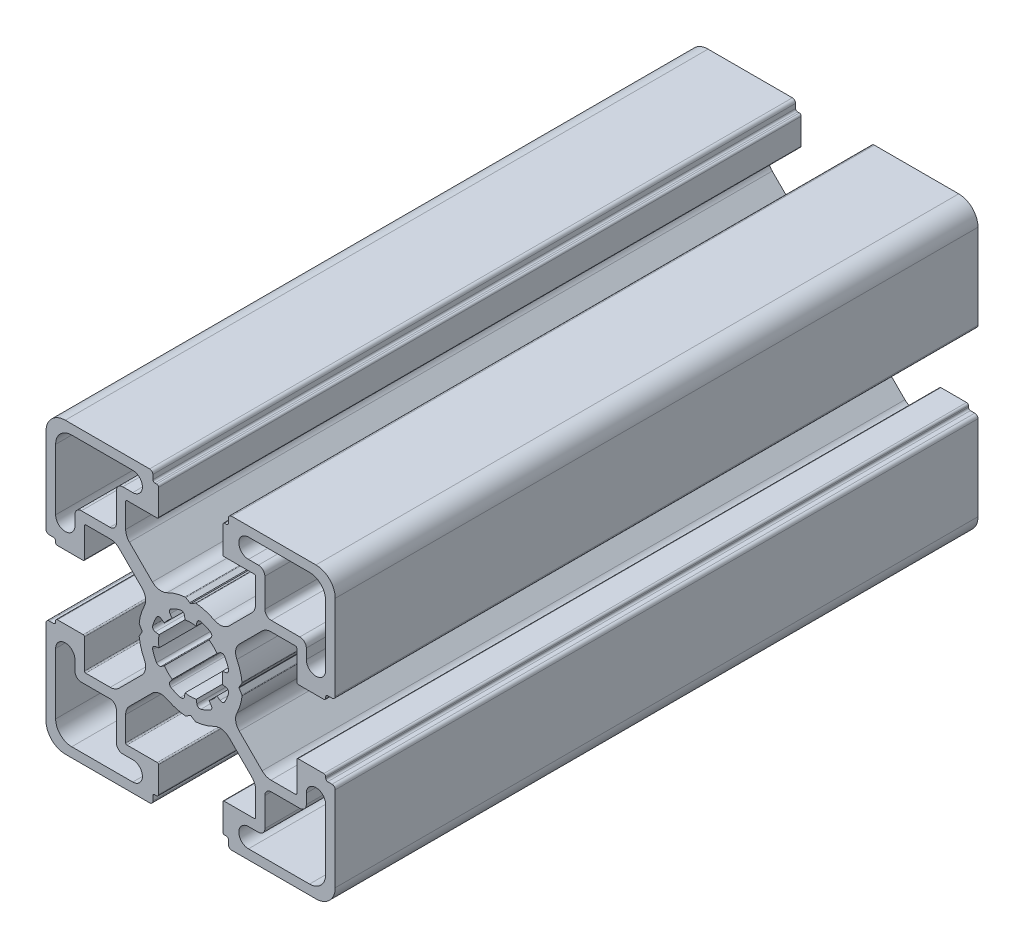
SolidWorks part; units mm, degrees
material "АД31 ГОСТ 4784-97"
ref_plane "Front Plane" through (0, 0, 0) normal (0, 0, 1) x (1, 0, 0)
ref_plane "Top Plane" through (0, 0, 0) normal (0, 1, 0) x (1, 0, 0)
ref_plane "Right Plane" through (0, 0, 0) normal (1, 0, 0) x (0, 0, -1)
sketch "Sketch1" plane through (0, 0, 0) normal (0, 0, 1) x (1, 0, 0)
  line L0 (10.55, 18) -> (9, 18)
  line L1 (18.5, 21) -> (9, 21)
  line L2 (21, 9.0002) -> (21, 18.5)
  line L3 (18, 9.0002) -> (18, 10.55)
  line L4 (17, 11.55) -> (12.55, 11.55)
  line L5 (11.55, 12.55) -> (11.55, 17)
  line L6 (7.974, 0.7926) -> (7.5401, 0.0468)
  line L7 (-0.8674, 4.9242) -> (-0.9675, 5.4811)
  line L8 (-3.1913, 4.5626) -> (-2.864, 4.0985)
  line L9 (-4.0897, 2.8765) -> (-4.5668, 3.2082)
  line L10 (-5.4897, 0.9862) -> (-4.9205, 0.8878)
  line L11 (11.1298, 9.425) -> (7.5635, 5.8587)
  line L12 (16.3169, 9.9945) -> (12.5048, 9.9945)
  line L13 (16.5169, 5.2) -> (16.5169, 9.7945)
  line L14 (20.7196, 5) -> (16.7169, 5)
  line L15 (21.0196, 5.3) -> (21.0196, 5.5)
  line L16 (22, 5.8) -> (21.3196, 5.8)
  line L17 (22.5, 6.3) -> (22.5, 19.5)
  line L18 (19.5, 22.5) -> (6.3757, 22.5)
  line L19 (5.8757, 21.3) -> (5.8757, 22)
  line L20 (5.5757, 21) -> (5.3, 21)
  line L21 (5, 16.6668) -> (5, 20.7)
  line L22 (9.9054, 16.4668) -> (5.2, 16.4668)
  line L23 (10.1054, 12.4716) -> (10.1054, 16.2668)
  line L24 (5.9449, 7.4827) -> (9.5196, 11.0574)
  line L25 (0.1126, 7.6069) -> (0.7547, 7.9748)
  line L26 (5.4897, 0.9862) -> (4.9205, 0.8878)
  line L27 (4.0897, 2.8765) -> (4.5668, 3.2082)
  line L28 (3.1913, 4.5626) -> (2.864, 4.0985)
  line L29 (0.8674, 4.9242) -> (0.9675, 5.4811)
  line L30 (-10.55, -18) -> (-9, -18)
  line L31 (-18.5, -21) -> (-9, -21)
  line L32 (-21, -9.0002) -> (-21, -18.5)
  line L33 (-18, -9.0002) -> (-18, -10.55)
  line L34 (-17, -11.55) -> (-12.55, -11.55)
  line L35 (-11.55, -12.55) -> (-11.55, -17)
  line L36 (-7.974, -0.7926) -> (-7.5401, -0.0468)
  line L37 (-11.1298, -9.425) -> (-7.5635, -5.8587)
  line L38 (-16.3169, -9.9945) -> (-12.5048, -9.9945)
  line L39 (-16.5169, -5.2) -> (-16.5169, -9.7945)
  line L40 (-20.7196, -5) -> (-16.7169, -5)
  line L41 (-21.0196, -5.3) -> (-21.0196, -5.5)
  line L42 (-22, -5.8) -> (-21.3196, -5.8)
  line L43 (-22.5, -6.3) -> (-22.5, -19.5)
  line L44 (-19.5, -22.5) -> (-6.3757, -22.5)
  line L45 (-5.8757, -21.3) -> (-5.8757, -22)
  line L46 (-5.5757, -21) -> (-5.3, -21)
  line L47 (-5, -16.6668) -> (-5, -20.7)
  line L48 (-9.9054, -16.4668) -> (-5.2, -16.4668)
  line L49 (-10.1054, -12.4716) -> (-10.1054, -16.2668)
  line L50 (-5.9449, -7.4827) -> (-9.5196, -11.0574)
  line L51 (-0.1126, -7.6069) -> (-0.7547, -7.9748)
  line L52 (0.8674, -4.9242) -> (0.9675, -5.4811)
  line L53 (3.1913, -4.5626) -> (2.864, -4.0985)
  line L54 (4.0897, -2.8765) -> (4.5668, -3.2082)
  line L55 (5.4897, -0.9862) -> (4.9205, -0.8878)
  line L56 (0.1126, -7.6069) -> (0.7547, -7.9748)
  line L57 (5.9449, -7.4827) -> (9.5196, -11.0574)
  line L58 (10.1054, -12.4716) -> (10.1054, -16.2668)
  line L59 (9.9054, -16.4668) -> (5.2, -16.4668)
  line L60 (5, -16.6668) -> (5, -20.7)
  line L61 (5.5757, -21) -> (5.3, -21)
  line L62 (-0.1126, 7.6069) -> (-0.7547, 7.9748)
  line L63 (-5.9449, 7.4827) -> (-9.5196, 11.0574)
  line L64 (-10.1054, 12.4716) -> (-10.1054, 16.2668)
  line L65 (-9.9054, 16.4668) -> (-5.2, 16.4668)
  line L66 (-5, 16.6668) -> (-5, 20.7)
  line L67 (-5.5757, 21) -> (-5.3, 21)
  line L68 (-5.8757, 21.3) -> (-5.8757, 22)
  line L69 (-19.5, 22.5) -> (-6.3757, 22.5)
  line L70 (-22.5, 6.3) -> (-22.5, 19.5)
  line L71 (-22, 5.8) -> (-21.3196, 5.8)
  line L72 (-21.0196, 5.3) -> (-21.0196, 5.5)
  line L73 (-20.7196, 5) -> (-16.7169, 5)
  line L74 (-16.5169, 5.2) -> (-16.5169, 9.7945)
  line L75 (-16.3169, 9.9945) -> (-12.5048, 9.9945)
  line L76 (-11.1298, 9.425) -> (-7.5635, 5.8587)
  line L77 (-7.974, 0.7926) -> (-7.5401, 0.0468)
  line L78 (5.8757, -21.3) -> (5.8757, -22)
  line L79 (19.5, -22.5) -> (6.3757, -22.5)
  line L80 (22.5, -6.3) -> (22.5, -19.5)
  line L81 (22, -5.8) -> (21.3196, -5.8)
  line L82 (21.0196, -5.3) -> (21.0196, -5.5)
  line L83 (20.7196, -5) -> (16.7169, -5)
  line L84 (16.5169, -5.2) -> (16.5169, -9.7945)
  line L85 (16.3169, -9.9945) -> (12.5048, -9.9945)
  line L86 (11.1298, -9.425) -> (7.5635, -5.8587)
  line L87 (-5.4897, -0.9862) -> (-4.9205, -0.8878)
  line L88 (-4.0897, -2.8765) -> (-4.5668, -3.2082)
  line L89 (-3.1913, -4.5626) -> (-2.864, -4.0985)
  line L90 (-0.8674, -4.9242) -> (-0.9675, -5.4811)
  line L91 (7.974, -0.7926) -> (7.5401, -0.0468)
  line L92 (-11.55, 12.55) -> (-11.55, 17)
  line L93 (-17, 11.55) -> (-12.55, 11.55)
  line L94 (-18, 9.0002) -> (-18, 10.55)
  line L95 (-21, 9.0002) -> (-21, 18.5)
  line L96 (-18.5, 21) -> (-9, 21)
  line L97 (-10.55, 18) -> (-9, 18)
  line L98 (11.55, -12.55) -> (11.55, -17)
  line L99 (17, -11.55) -> (12.55, -11.55)
  line L100 (18, -9.0002) -> (18, -10.55)
  line L101 (21, -9.0002) -> (21, -18.5)
  line L102 (18.5, -21) -> (9, -21)
  line L103 (10.55, -18) -> (9, -18)
  line L104 (-33.3633, 0) -> (37.7265, 0) construction
  line L105 (0, 32.2957) -> (0, -36.0465) construction
  arc A0 (9, 18) -> (9, 21) centre (9, 19.5) cw
  arc A1 (18.5, 21) -> (21, 18.5) centre (18.5, 18.5) cw
  arc A2 (21, 9.0002) -> (18, 9.0002) centre (19.5, 9.0002) cw
  arc A3 (17, 11.55) -> (18, 10.55) centre (17, 10.55) cw
  arc A4 (12.55, 11.55) -> (11.55, 12.55) centre (12.55, 12.55) cw
  arc A5 (10.55, 18) -> (11.55, 17) centre (10.55, 17) cw
  arc A6 (7.5313, 0) -> (7.5401, 0.0468) centre (7.7309, -0.013) cw
  arc A7 (8, 0.9141) -> (7.974, 0.7926) centre (7.8011, 0.8932) cw
  arc A8 (7.2004, 3.6119) -> (8, 0.9141) centre (0.0496, 0.0249) cw
  arc A9 (7.2004, 3.6119) -> (7.5635, 5.8587) centre (8.9385, 4.4837) cw
  arc A10 (11.1298, 9.425) -> (12.5048, 9.9945) centre (12.5048, 8.05) cw
  arc A11 (16.3169, 9.9945) -> (16.5169, 9.7945) centre (16.3169, 9.7945) cw
  arc A12 (16.7169, 5) -> (16.5169, 5.2) centre (16.7169, 5.2) cw
  arc A13 (21.0196, 5.3) -> (20.7196, 5) centre (20.7196, 5.3) cw
  arc A14 (0.8674, 4.9242) -> (-0.8674, 4.9242) centre (0, 0) ccw
  arc A15 (-0.9675, 5.4811) -> (-1.5951, 5.8941) centre (-1.4627, 5.4119) ccw
  arc A16 (-1.5951, 5.8941) -> (-3.0444, 5.2994) centre (-0.0235, 0) ccw
  arc A17 (-3.0444, 5.2994) -> (-3.1913, 4.5626) centre (-2.7943, 4.8665) ccw
  arc A18 (-2.864, 4.0985) -> (-4.0897, 2.8765) centre (0, 0) ccw
  arc A19 (-4.5668, 3.2082) -> (-5.3025, 3.0565) centre (-4.868, 2.8091) ccw
  arc A20 (-5.3025, 3.0565) -> (-5.9068, 1.6112) centre (-0.0235, 0) ccw
  arc A21 (-5.9068, 1.6112) -> (-5.4897, 0.9862) centre (-5.4239, 1.4819) ccw
  arc A22 (-4.9205, 0.8878) -> (-5, 0) centre (0, 0) ccw
  arc A23 (21.0196, 5.5) -> (21.3196, 5.8) centre (21.3196, 5.5) cw
  arc A24 (22.5, 6.3) -> (22, 5.8) centre (22, 6.3) cw
  arc A25 (19.5, 22.5) -> (22.5, 19.5) centre (19.5, 19.5) cw
  arc A26 (5.8757, 22) -> (6.3757, 22.5) centre (6.3757, 22) cw
  arc A27 (5.8757, 21.3) -> (5.5757, 21) centre (5.5757, 21.3) cw
  arc A28 (5, 20.7) -> (5.3, 21) centre (5.3, 20.7) cw
  arc A29 (5.2, 16.4668) -> (5, 16.6668) centre (5.2, 16.6668) cw
  arc A30 (9.9054, 16.4668) -> (10.1054, 16.2668) centre (9.9054, 16.2668) cw
  arc A31 (10.1054, 12.4716) -> (9.5196, 11.0574) centre (8.1054, 12.4716) cw
  arc A32 (5.9449, 7.4827) -> (3.6665, 7.1733) centre (4.5855, 8.9496) cw
  arc A33 (0.8764, 8) -> (3.6665, 7.1733) centre (0.0235, 0) cw
  arc A34 (0.7547, 7.9748) -> (0.8764, 8) centre (0.8542, 7.8013) cw
  arc A35 (0.1126, 7.6069) -> (0, 7.531) centre (-0.0489, 7.7249) cw
  arc A36 (4.9205, 0.8878) -> (5, 0) centre (0, 0) cw
  arc A37 (5.9068, 1.6112) -> (5.4897, 0.9862) centre (5.4239, 1.4819) cw
  arc A38 (5.3025, 3.0565) -> (5.9068, 1.6112) centre (0.0235, 0) cw
  arc A39 (4.5668, 3.2082) -> (5.3025, 3.0565) centre (4.868, 2.8091) cw
  arc A40 (2.864, 4.0985) -> (4.0897, 2.8765) centre (0, 0) cw
  arc A41 (3.0444, 5.2994) -> (3.1913, 4.5626) centre (2.7943, 4.8665) cw
  arc A42 (1.5951, 5.8941) -> (3.0444, 5.2994) centre (0.0235, 0) cw
  arc A43 (0.9675, 5.4811) -> (1.5951, 5.8941) centre (1.4627, 5.4119) cw
  arc A44 (-9, -18) -> (-9, -21) centre (-9, -19.5) cw
  arc A45 (-18.5, -21) -> (-21, -18.5) centre (-18.5, -18.5) cw
  arc A46 (-21, -9.0002) -> (-18, -9.0002) centre (-19.5, -9.0002) cw
  arc A47 (-17, -11.55) -> (-18, -10.55) centre (-17, -10.55) cw
  arc A48 (-12.55, -11.55) -> (-11.55, -12.55) centre (-12.55, -12.55) cw
  arc A49 (-10.55, -18) -> (-11.55, -17) centre (-10.55, -17) cw
  arc A50 (-7.5313, 0) -> (-7.5401, -0.0468) centre (-7.7309, 0.013) cw
  arc A51 (-8, -0.9141) -> (-7.974, -0.7926) centre (-7.8011, -0.8932) cw
  arc A52 (-7.2004, -3.6119) -> (-8, -0.9141) centre (-0.0496, -0.0249) cw
  arc A53 (-7.2004, -3.6119) -> (-7.5635, -5.8587) centre (-8.9385, -4.4837) cw
  arc A54 (-11.1298, -9.425) -> (-12.5048, -9.9945) centre (-12.5048, -8.05) cw
  arc A55 (-16.3169, -9.9945) -> (-16.5169, -9.7945) centre (-16.3169, -9.7945) cw
  arc A56 (-16.7169, -5) -> (-16.5169, -5.2) centre (-16.7169, -5.2) cw
  arc A57 (-21.0196, -5.3) -> (-20.7196, -5) centre (-20.7196, -5.3) cw
  arc A58 (-21.0196, -5.5) -> (-21.3196, -5.8) centre (-21.3196, -5.5) cw
  arc A59 (-22.5, -6.3) -> (-22, -5.8) centre (-22, -6.3) cw
  arc A60 (-19.5, -22.5) -> (-22.5, -19.5) centre (-19.5, -19.5) cw
  arc A61 (-5.8757, -22) -> (-6.3757, -22.5) centre (-6.3757, -22) cw
  arc A62 (-5.8757, -21.3) -> (-5.5757, -21) centre (-5.5757, -21.3) cw
  arc A63 (-5, -20.7) -> (-5.3, -21) centre (-5.3, -20.7) cw
  arc A64 (-5.2, -16.4668) -> (-5, -16.6668) centre (-5.2, -16.6668) cw
  arc A65 (-9.9054, -16.4668) -> (-10.1054, -16.2668) centre (-9.9054, -16.2668) cw
  arc A66 (-10.1054, -12.4716) -> (-9.5196, -11.0574) centre (-8.1054, -12.4716) cw
  arc A67 (-5.9449, -7.4827) -> (-3.6665, -7.1733) centre (-4.5855, -8.9496) cw
  arc A68 (-0.8764, -8) -> (-3.6665, -7.1733) centre (-0.0235, 0) cw
  arc A69 (-0.7547, -7.9748) -> (-0.8764, -8) centre (-0.8542, -7.8013) cw
  arc A70 (-0.1126, -7.6069) -> (0, -7.531) centre (0.0489, -7.7249) cw
  arc A71 (0.9675, -5.4811) -> (1.5951, -5.8941) centre (1.4627, -5.4119) ccw
  arc A72 (1.5951, -5.8941) -> (3.0444, -5.2994) centre (0.0235, 0) ccw
  arc A73 (3.0444, -5.2994) -> (3.1913, -4.5626) centre (2.7943, -4.8665) ccw
  arc A74 (2.864, -4.0985) -> (4.0897, -2.8765) centre (0, 0) ccw
  arc A75 (4.5668, -3.2082) -> (5.3025, -3.0565) centre (4.868, -2.8091) ccw
  arc A76 (5.3025, -3.0565) -> (5.9068, -1.6112) centre (0.0235, 0) ccw
  arc A77 (5.9068, -1.6112) -> (5.4897, -0.9862) centre (5.4239, -1.4819) ccw
  arc A78 (4.9205, -0.8878) -> (5, 0) centre (0, 0) ccw
  arc A79 (0.1126, -7.6069) -> (0, -7.531) centre (-0.0489, -7.7249) ccw
  arc A80 (0.7547, -7.9748) -> (0.8764, -8) centre (0.8542, -7.8013) ccw
  arc A81 (0.8764, -8) -> (3.6665, -7.1733) centre (0.0235, 0) ccw
  arc A82 (5.9449, -7.4827) -> (3.6665, -7.1733) centre (4.5855, -8.9496) ccw
  arc A83 (10.1054, -12.4716) -> (9.5196, -11.0574) centre (8.1054, -12.4716) ccw
  arc A84 (9.9054, -16.4668) -> (10.1054, -16.2668) centre (9.9054, -16.2668) ccw
  arc A85 (5.2, -16.4668) -> (5, -16.6668) centre (5.2, -16.6668) ccw
  arc A86 (5, -20.7) -> (5.3, -21) centre (5.3, -20.7) ccw
  arc A87 (5.8757, -21.3) -> (5.5757, -21) centre (5.5757, -21.3) ccw
  arc A88 (-0.1126, 7.6069) -> (0, 7.531) centre (0.0489, 7.7249) ccw
  arc A89 (-0.7547, 7.9748) -> (-0.8764, 8) centre (-0.8542, 7.8013) ccw
  arc A90 (-0.8764, 8) -> (-3.6665, 7.1733) centre (-0.0235, 0) ccw
  arc A91 (-5.9449, 7.4827) -> (-3.6665, 7.1733) centre (-4.5855, 8.9496) ccw
  arc A92 (-10.1054, 12.4716) -> (-9.5196, 11.0574) centre (-8.1054, 12.4716) ccw
  arc A93 (-9.9054, 16.4668) -> (-10.1054, 16.2668) centre (-9.9054, 16.2668) ccw
  arc A94 (-5.2, 16.4668) -> (-5, 16.6668) centre (-5.2, 16.6668) ccw
  arc A95 (-5, 20.7) -> (-5.3, 21) centre (-5.3, 20.7) ccw
  arc A96 (-5.8757, 21.3) -> (-5.5757, 21) centre (-5.5757, 21.3) ccw
  arc A97 (-5.8757, 22) -> (-6.3757, 22.5) centre (-6.3757, 22) ccw
  arc A98 (-19.5, 22.5) -> (-22.5, 19.5) centre (-19.5, 19.5) ccw
  arc A99 (-22.5, 6.3) -> (-22, 5.8) centre (-22, 6.3) ccw
  arc A100 (-21.0196, 5.5) -> (-21.3196, 5.8) centre (-21.3196, 5.5) ccw
  arc A101 (-21.0196, 5.3) -> (-20.7196, 5) centre (-20.7196, 5.3) ccw
  arc A102 (-16.7169, 5) -> (-16.5169, 5.2) centre (-16.7169, 5.2) ccw
  arc A103 (-16.3169, 9.9945) -> (-16.5169, 9.7945) centre (-16.3169, 9.7945) ccw
  arc A104 (-11.1298, 9.425) -> (-12.5048, 9.9945) centre (-12.5048, 8.05) ccw
  arc A105 (-7.2004, 3.6119) -> (-7.5635, 5.8587) centre (-8.9385, 4.4837) ccw
  arc A106 (-7.2004, 3.6119) -> (-8, 0.9141) centre (-0.0496, 0.0249) ccw
  arc A107 (-8, 0.9141) -> (-7.974, 0.7926) centre (-7.8011, 0.8932) ccw
  arc A108 (-7.5313, 0) -> (-7.5401, 0.0468) centre (-7.7309, -0.013) ccw
  arc A109 (5.8757, -22) -> (6.3757, -22.5) centre (6.3757, -22) ccw
  arc A110 (19.5, -22.5) -> (22.5, -19.5) centre (19.5, -19.5) ccw
  arc A111 (22.5, -6.3) -> (22, -5.8) centre (22, -6.3) ccw
  arc A112 (21.0196, -5.5) -> (21.3196, -5.8) centre (21.3196, -5.5) ccw
  arc A113 (-4.9205, -0.8878) -> (-5, 0) centre (0, 0) cw
  arc A114 (-5.9068, -1.6112) -> (-5.4897, -0.9862) centre (-5.4239, -1.4819) cw
  arc A115 (-5.3025, -3.0565) -> (-5.9068, -1.6112) centre (-0.0235, 0) cw
  arc A116 (-4.5668, -3.2082) -> (-5.3025, -3.0565) centre (-4.868, -2.8091) cw
  arc A117 (-2.864, -4.0985) -> (-4.0897, -2.8765) centre (0, 0) cw
  arc A118 (-3.0444, -5.2994) -> (-3.1913, -4.5626) centre (-2.7943, -4.8665) cw
  arc A119 (-1.5951, -5.8941) -> (-3.0444, -5.2994) centre (-0.0235, 0) cw
  arc A120 (-0.9675, -5.4811) -> (-1.5951, -5.8941) centre (-1.4627, -5.4119) cw
  arc A121 (0.8674, -4.9242) -> (-0.8674, -4.9242) centre (0, 0) cw
  arc A122 (21.0196, -5.3) -> (20.7196, -5) centre (20.7196, -5.3) ccw
  arc A123 (16.7169, -5) -> (16.5169, -5.2) centre (16.7169, -5.2) ccw
  arc A124 (-10.55, 18) -> (-11.55, 17) centre (-10.55, 17) ccw
  arc A125 (-12.55, 11.55) -> (-11.55, 12.55) centre (-12.55, 12.55) ccw
  arc A126 (-17, 11.55) -> (-18, 10.55) centre (-17, 10.55) ccw
  arc A127 (-21, 9.0002) -> (-18, 9.0002) centre (-19.5, 9.0002) ccw
  arc A128 (-18.5, 21) -> (-21, 18.5) centre (-18.5, 18.5) ccw
  arc A129 (-9, 18) -> (-9, 21) centre (-9, 19.5) ccw
  arc A130 (16.3169, -9.9945) -> (16.5169, -9.7945) centre (16.3169, -9.7945) ccw
  arc A131 (11.1298, -9.425) -> (12.5048, -9.9945) centre (12.5048, -8.05) ccw
  arc A132 (7.2004, -3.6119) -> (7.5635, -5.8587) centre (8.9385, -4.4837) ccw
  arc A133 (7.2004, -3.6119) -> (8, -0.9141) centre (0.0496, -0.0249) ccw
  arc A134 (8, -0.9141) -> (7.974, -0.7926) centre (7.8011, -0.8932) ccw
  arc A135 (7.5313, 0) -> (7.5401, -0.0468) centre (7.7309, 0.013) ccw
  arc A136 (10.55, -18) -> (11.55, -17) centre (10.55, -17) ccw
  arc A137 (12.55, -11.55) -> (11.55, -12.55) centre (12.55, -12.55) ccw
  arc A138 (17, -11.55) -> (18, -10.55) centre (17, -10.55) ccw
  arc A139 (21, -9.0002) -> (18, -9.0002) centre (19.5, -9.0002) ccw
  arc A140 (18.5, -21) -> (21, -18.5) centre (18.5, -18.5) ccw
  arc A141 (9, -18) -> (9, -21) centre (9, -19.5) ccw
  dimension "D6" = 12.2
  dimension "D8" = 10
  dimension "D1" = 10
  dimension "D2" = 45
  dimension "D3" = 45
  dimension "D4" = 10
  dimension "D5" = 14.5
  dimension "D7" = 22.5
extrude "Base-Extrude" add sketch "Sketch1" against normal blind 100
